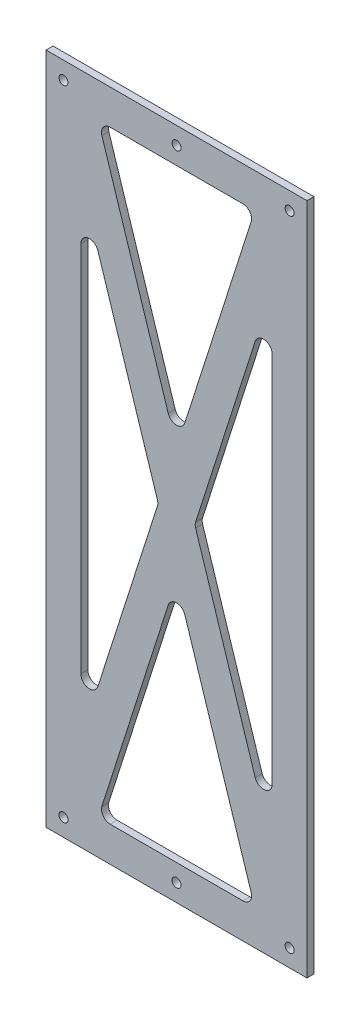
SolidWorks part; units mm, degrees
ref_plane "前视基准面" through (0, 0, 0) normal (0, 0, 1) x (1, 0, 0)
ref_plane "上视基准面" through (0, 0, 0) normal (0, 1, 0) x (1, 0, 0)
ref_plane "右视基准面" through (0, 0, 0) normal (1, 0, 0) x (0, 0, -1)
sketch "Sketch2" plane through (0, 0, 30) normal (0, 0, 1) x (1, 0, 0)
  line L0 (-470, 10) -> (-10, 10) construction
  line L1 (-200, 10) -> (-50, 10)
  line L2 (-200, 10) -> (-200, -377)
  line L3 (-200, -377) -> (-50, -377)
  line L4 (-50, 10) -> (-50, -377)
  line L5 (-10, -377) -> (-470, -377) construction
  line L6 (-10, -10) -> (-10, 10) construction
  line L7 (-200, -183.5) -> (-50, -183.5) construction
  line L8 (-190, 0) -> (-60, 0) construction
  circle A0 centre (-190, 0) radius 2.6
  circle A1 centre (-60, 0) radius 2.6
  circle A2 centre (-125, 0) radius 2.6
  circle A3 centre (-60, -367) radius 2.6
  circle A4 centre (-125, -367) radius 2.6
  circle A5 centre (-190, -367) radius 2.6
  dimension "D3" = 5.2
  dimension "D5" = 10
  dimension "D1" = 40
  dimension "D2" = 150
  dimension "D4" = 10
extrude "Boss-Extrude1" add sketch "Sketch2" along normal blind 4
sketch "Sketch3" plane through (0, 0, 34) normal (0, 0, 1) x (1, 0, 0)
  line L0 (-200, -377) -> (-50, -377) construction
  line L1 (-163.151, -10) -> (-86.849, -10)
  line L2 (-180, -76.4246) -> (-180, -290.5754)
  line L3 (-163.151, -357) -> (-86.849, -357)
  line L4 (-70, -76.4246) -> (-70, -290.5754)
  line L5 (-50, 10) -> (-200, 10) construction
  line L6 (-200, 10) -> (-200, -377) construction
  line L7 (-50, -377) -> (-50, 10) construction
  line L8 (-167.9133, -16.5234) -> (-129.7623, -135.7901)
  line L10 (-82.0867, -350.4766) -> (-120.2377, -231.2099)
  line L11 (-170.2377, -292.0988) -> (-135.9864, -185.0234)
  line L13 (-79.7623, -74.9012) -> (-114.0136, -181.9766)
  line L14 (-114.0136, -185.0234) -> (-79.7623, -292.0988)
  line L15 (-135.9864, -181.9766) -> (-170.2377, -74.9012)
  line L16 (-120.2377, -135.7901) -> (-82.0867, -16.5234)
  line L17 (-129.7623, -231.2099) -> (-167.9133, -350.4766)
  arc A0 (-86.849, -357) -> (-82.0867, -350.4766) centre (-86.849, -352) ccw
  arc A1 (-163.151, -357) -> (-167.9133, -350.4766) centre (-163.151, -352) cw
  arc A2 (-170.2377, -292.0988) -> (-180, -290.5754) centre (-175, -290.5754) cw
  arc A3 (-79.7623, -292.0988) -> (-70, -290.5754) centre (-75, -290.5754) ccw
  arc A4 (-120.2377, -231.2099) -> (-129.7623, -231.2099) centre (-125, -232.7333) ccw
  arc A5 (-135.9864, -181.9766) -> (-135.9864, -185.0234) centre (-140.7487, -183.5) cw
  arc A6 (-170.2377, -74.9012) -> (-180, -76.4246) centre (-175, -76.4246) ccw
  arc A7 (-70, -76.4246) -> (-79.7623, -74.9012) centre (-75, -76.4246) ccw
  arc A8 (-114.0136, -185.0234) -> (-114.0136, -181.9766) centre (-109.2513, -183.5) cw
  arc A9 (-82.0867, -16.5234) -> (-86.849, -10) centre (-86.849, -15) ccw
  arc A10 (-129.7623, -135.7901) -> (-120.2377, -135.7901) centre (-125, -134.2667) ccw
  arc A11 (-167.9133, -16.5234) -> (-163.151, -10) centre (-163.151, -15) cw
  point P31 (-125, -216.3222)
  point P42 (-80, -10)
  point P45 (-125, -150.6778)
  dimension "D8" = 5
  dimension "D1" = 20
  dimension "D2" = 20
  dimension "D3" = 20
  dimension "D4" = 20
  dimension "D5" = 20
  dimension "D6" = 20
  dimension "D7" = 10
extrude "Cut-Extrude1" cut sketch "Sketch3" against normal blind 10
